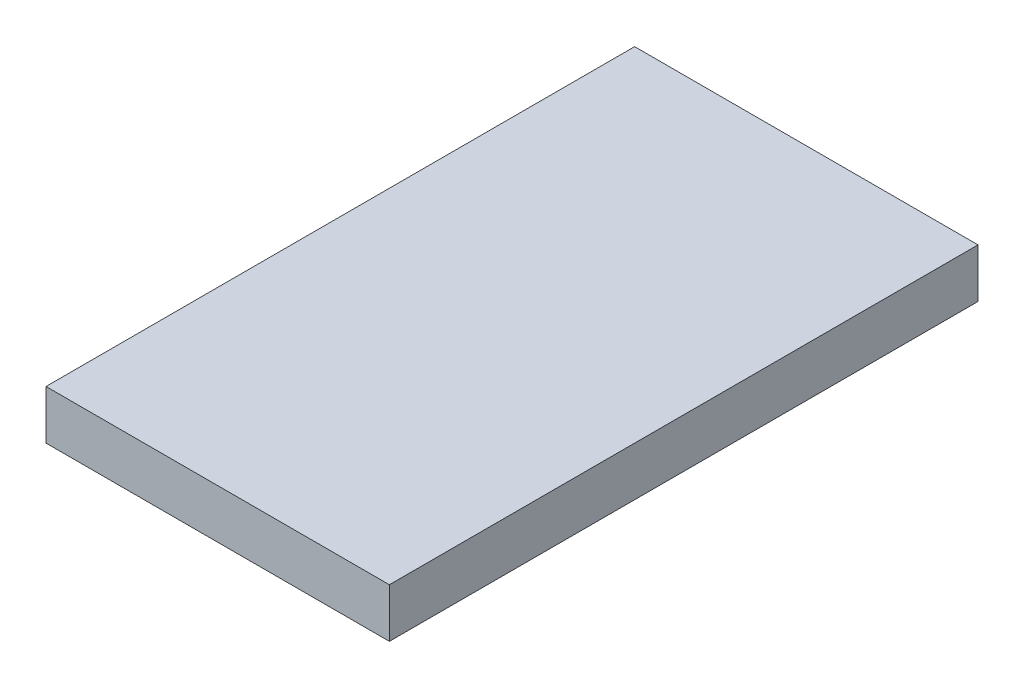
SolidWorks part; units mm, degrees
ref_plane "Plano frontal" through (0, 0, 0) normal (0, 0, 1) x (1, 0, 0)
ref_plane "Plano superior" through (0, 0, 0) normal (0, 1, 0) x (1, 0, 0)
ref_plane "Plano direito" through (0, 0, 0) normal (1, 0, 0) x (0, 0, -1)
sketch "Esboço1" plane through (0, 0, 0) normal (0, 0, 1) x (1, 0, 0)
  line L1 (0, 0) -> (700, 0)
  line L2 (0, 0) -> (0, 100)
  line L3 (0, 100) -> (700, 100)
  line L4 (700, 0) -> (700, 100)
  dimension "D1" = 700
  dimension "D2" = 100
extrude "Ressalto-extrusão1" add sketch "Esboço1" along normal blind 1200
